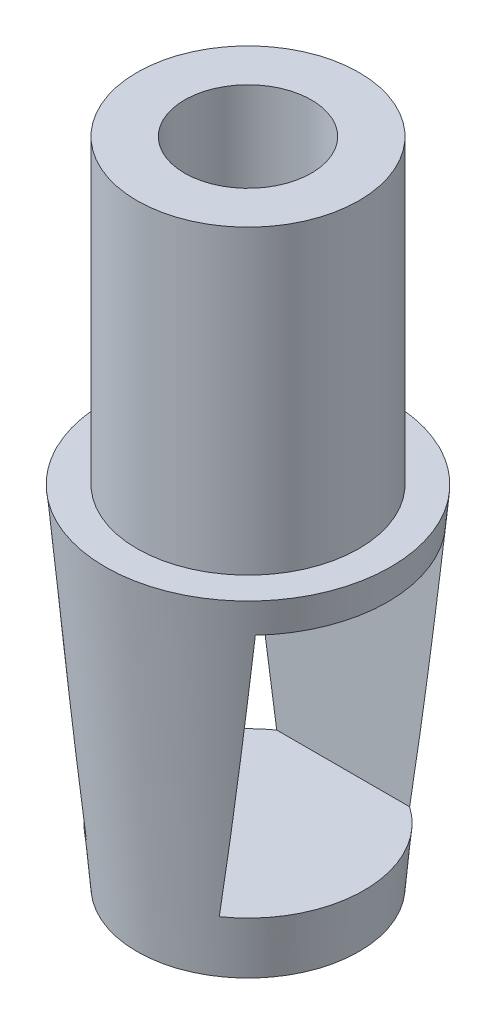
SolidWorks part; units mm, degrees
ref_plane "Front Plane" through (0, 0, 0) normal (0, 0, 1) x (1, 0, 0)
ref_plane "Top Plane" through (0, 0, 0) normal (0, 1, 0) x (1, 0, 0)
ref_plane "Right Plane" through (0, 0, 0) normal (1, 0, 0) x (0, 0, -1)
sketch "Sketch1" plane through (0, 0, 0) normal (1, 0, 0) x (0, 0, -1)
  line L0 (0, 13.9245) -> (0, -13.9245) construction
  line L1 (4, 19) -> (7, 19)
  line L2 (7, 19) -> (7, 0)
  line L3 (7, 0) -> (4, 0)
  line L4 (4, 0) -> (4, 19)
  line L5 (0, 0) -> (9, 0)
  line L6 (9, 0) -> (7, -22)
  line L7 (7, -22) -> (0, -22)
  line L8 (0, -22) -> (0, 0)
  point P3 (0, 0)
  dimension "D1" = 4
  dimension "D2" = 7
  dimension "D3" = 19
  dimension "D4" = 22
  dimension "D5" = 7
  dimension "D6" = 9
revolve "Revolve1" add sketch "Sketch1" angle 360 about L0
sketch "Sketch2" plane through (0, 0, 0) normal (1, 0, 0) x (0, 0, -1)
  line L0 (-7, -22) -> (7, -22) construction
  line L1 (-6, -2) -> (6, -2)
  line L2 (-6, -2) -> (-6, -18.5)
  line L3 (-6, -18.5) -> (6, -18.5)
  line L4 (6, -2) -> (6, -18.5)
  line L5 (-6, -2) -> (6, -18.5) construction
  line L6 (-6, -18.5) -> (6, -2) construction
  line L7 (0, 0) -> (0, -10.25) construction
  point P0 (0, -10.25)
  dimension "D1" = 12
  dimension "D2" = 16.5
  dimension "D3" = 3.5
extrude "Cut-Extrude1" cut sketch "Sketch2" against normal through all both and the other way through all
